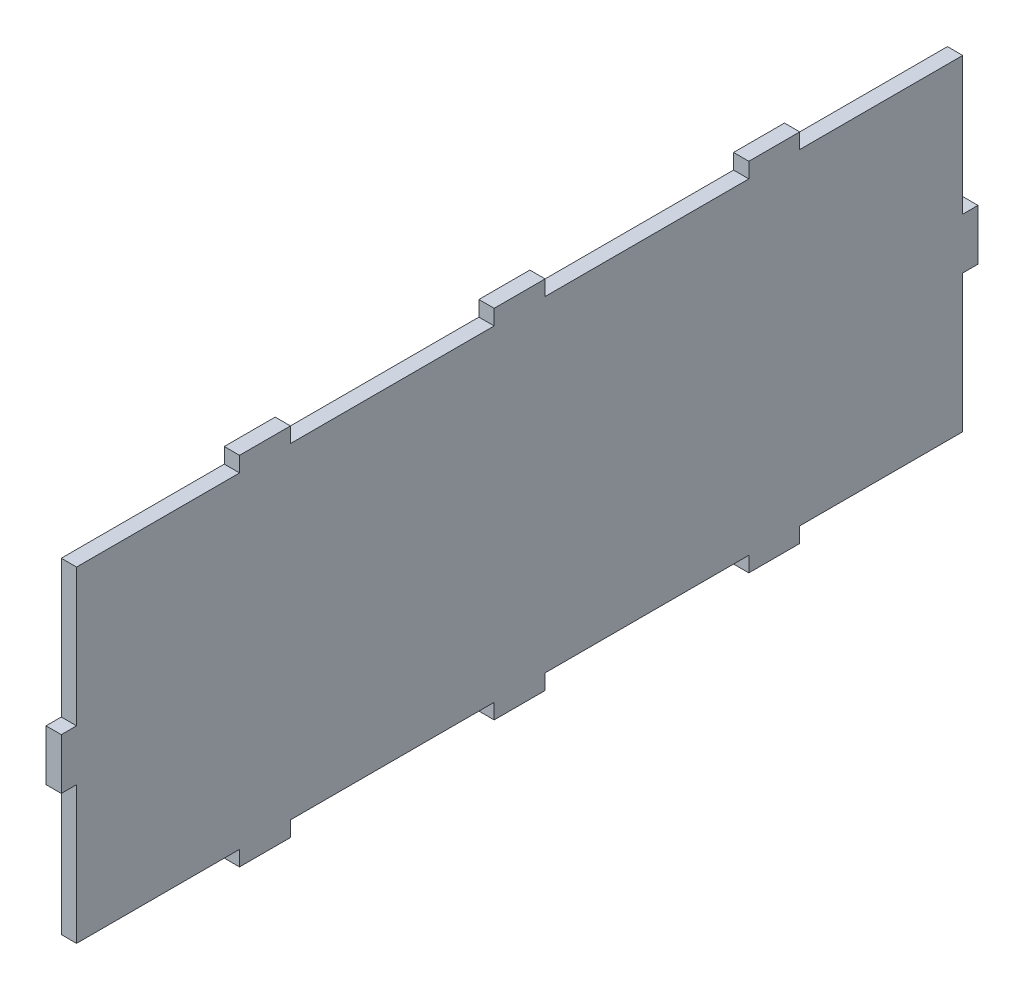
SolidWorks part; units mm, degrees
ref_plane "Front Plane" through (0, 0, 0) normal (0, 0, 1) x (1, 0, 0)
ref_plane "Top Plane" through (0, 0, 0) normal (0, 1, 0) x (1, 0, 0)
ref_plane "Right Plane" through (0, 0, 0) normal (1, 0, 0) x (0, 0, -1)
sketch "Sketch1" plane through (0, 0, 0) normal (1, 0, 0) x (0, 0, -1)
  line L1 (-90, 35) -> (90, 35)
  line L2 (-90, 35) -> (-90, -35)
  line L3 (-90, -35) -> (90, -35)
  line L4 (90, 35) -> (90, -35)
  line L5 (-90, 35) -> (90, -35) construction
  line L6 (-90, -35) -> (90, 35) construction
  point P0 (0, 0)
  dimension "D1" = 180
  dimension "D2" = 70
extrude "Boss-Extrude1" add sketch "Sketch1" along normal blind 3
sketch "Sketch2" plane through (3, 0, 0) normal (1, 0, 0) x (0, 0, -1)
  line L0 (0, 0) -> (0, 35)
  line L1 (90, 35) -> (-90, 35) construction
  line L3 (-90, -35) -> (90, -35) construction
  line L4 (0, 0) -> (90, 0)
  line L5 (90, -35) -> (90, 35) construction
  line L7 (-90, 35) -> (-90, -35) construction
  line L8 (-5, 35) -> (-45, 35)
  line L9 (0, 35) -> (5, 35)
  line L10 (0, 35) -> (0, 32)
  line L11 (0, 32) -> (5, 32)
  line L12 (5, 35) -> (5, 32)
  line L13 (0, 35) -> (-5, 35)
  line L14 (0, 35) -> (0, 32)
  line L15 (0, 32) -> (-5, 32)
  line L16 (-5, 35) -> (-5, 32)
  line L17 (0, -35) -> (5, -35)
  line L18 (0, -35) -> (0, -32)
  line L19 (0, -32) -> (5, -32)
  line L20 (5, -35) -> (5, -32)
  line L21 (0, -35) -> (-5, -35)
  line L22 (0, -35) -> (0, -32)
  line L23 (0, -32) -> (-5, -32)
  line L24 (-5, -35) -> (-5, -32)
  line L25 (90, 0) -> (87, 0)
  line L26 (90, 0) -> (90, 5)
  line L27 (90, 5) -> (87, 5)
  line L28 (87, 0) -> (87, 5)
  line L29 (87, 0) -> (90, 0)
  line L30 (87, 0) -> (87, -5)
  line L31 (87, -5) -> (90, -5)
  line L32 (90, 0) -> (90, -5)
  line L33 (-90, 0) -> (-87, 0)
  line L34 (-90, 0) -> (-90, 5)
  line L35 (-90, 5) -> (-87, 5)
  line L36 (-87, 0) -> (-87, 5)
  line L37 (-90, 0) -> (-87, 0)
  line L38 (-90, 0) -> (-90, -5)
  line L39 (-90, -5) -> (-87, -5)
  line L40 (-87, 0) -> (-87, -5)
  line L41 (-90, 5) -> (-87, 5)
  line L42 (-90, 5) -> (-90, 32)
  line L43 (-90, 32) -> (-87, 32)
  line L44 (-87, 5) -> (-87, 32)
  line L45 (-90, -5) -> (-87, -5)
  line L46 (-90, -5) -> (-90, -32)
  line L47 (-90, -32) -> (-87, -32)
  line L48 (-87, -5) -> (-87, -32)
  line L49 (90, 32) -> (87, 32)
  line L50 (90, 32) -> (90, 5)
  line L51 (90, 5) -> (87, 5)
  line L52 (87, 32) -> (87, 5)
  line L53 (90, -5) -> (87, -5)
  line L54 (90, -5) -> (90, -32)
  line L55 (90, -32) -> (87, -32)
  line L56 (87, -5) -> (87, -32)
  line L74 (-45, 35) -> (-55, 35)
  line L75 (-45, 35) -> (-45, 32)
  line L76 (-45, 32) -> (-55, 32)
  line L77 (-55, 35) -> (-55, 32)
  line L80 (45, 35) -> (45, 32)
  line L81 (45, 32) -> (55, 32)
  line L82 (55, 35) -> (55, 32)
  line L83 (-55, -35) -> (-45, -35)
  line L84 (-55, -35) -> (-55, -32)
  line L85 (-55, -32) -> (-45, -32)
  line L86 (-45, -35) -> (-45, -32)
  line L87 (45, -35) -> (55, -35)
  line L88 (45, -35) -> (45, -32)
  line L89 (45, -32) -> (55, -32)
  line L90 (55, -35) -> (55, -32)
  line L91 (-55, -35) -> (-90, -35)
  line L92 (-55, -35) -> (-55, -32)
  line L93 (-55, -32) -> (-90, -32)
  line L94 (-90, -35) -> (-90, -32)
  line L95 (-5, -35) -> (-45, -35)
  line L96 (-5, -35) -> (-5, -32)
  line L97 (-5, -32) -> (-45, -32)
  line L98 (-45, -35) -> (-45, -32)
  line L99 (45, -35) -> (5, -35)
  line L100 (45, -35) -> (45, -32)
  line L101 (45, -32) -> (5, -32)
  line L102 (5, -35) -> (5, -32)
  line L103 (90, -35) -> (55, -35)
  line L104 (90, -35) -> (90, -32)
  line L105 (90, -32) -> (55, -32)
  line L106 (55, -35) -> (55, -32)
  line L107 (90, 32) -> (55, 32)
  line L108 (90, 32) -> (90, 35)
  line L110 (55, 32) -> (55, 35)
  line L111 (45, 32) -> (5, 32)
  line L112 (45, 32) -> (45, 35)
  line L114 (5, 32) -> (5, 35)
  line L115 (-5, 32) -> (-45, 32)
  line L116 (-5, 32) -> (-5, 35)
  line L117 (-5, 35) -> (-45, 35)
  line L118 (-45, 32) -> (-45, 35)
  line L119 (-55, 32) -> (-90, 32)
  line L120 (-55, 32) -> (-55, 35)
  line L121 (-55, 35) -> (-90, 35)
  line L122 (-90, 32) -> (-90, 35)
  line M16 (90, -35) -> (90, 35)
  line M17 (90, 35) -> (-90, 35)
  line M18 (-90, 35) -> (-90, -35)
  line M19 (-90, -35) -> (90, -35)
  dimension "D1" = 3
  dimension "D2" = 5
  dimension "D3" = 5
  dimension "D4" = 5
  dimension "D5" = 3
  dimension "D6" = 5
  dimension "D7" = 5
  dimension "D8" = 3
  dimension "D9" = 3
  dimension "D10" = 5
  dimension "D11" = 40
  dimension "D12" = 10
  dimension "D13" = 3
  dimension "D15" = 10
extrude "Cut-Extrude6" cut sketch "Sketch2" against normal blind 10 contours L55 L105 L90 M19 M16 | L31 L56 L55 M16 | L88 L101 L20 M19 | L24 L97 L86 M19 | L84 L93 L47 M18 M19 | L48 L39 L47 M18 | L35 L44 L43 M18 | L119 L77 L43 M17 M18 | L115 L16 L75 M17 | L111 L80 L12 M17 | L107 L49 L82 M16 M17 | L49 L52 L27 M16
